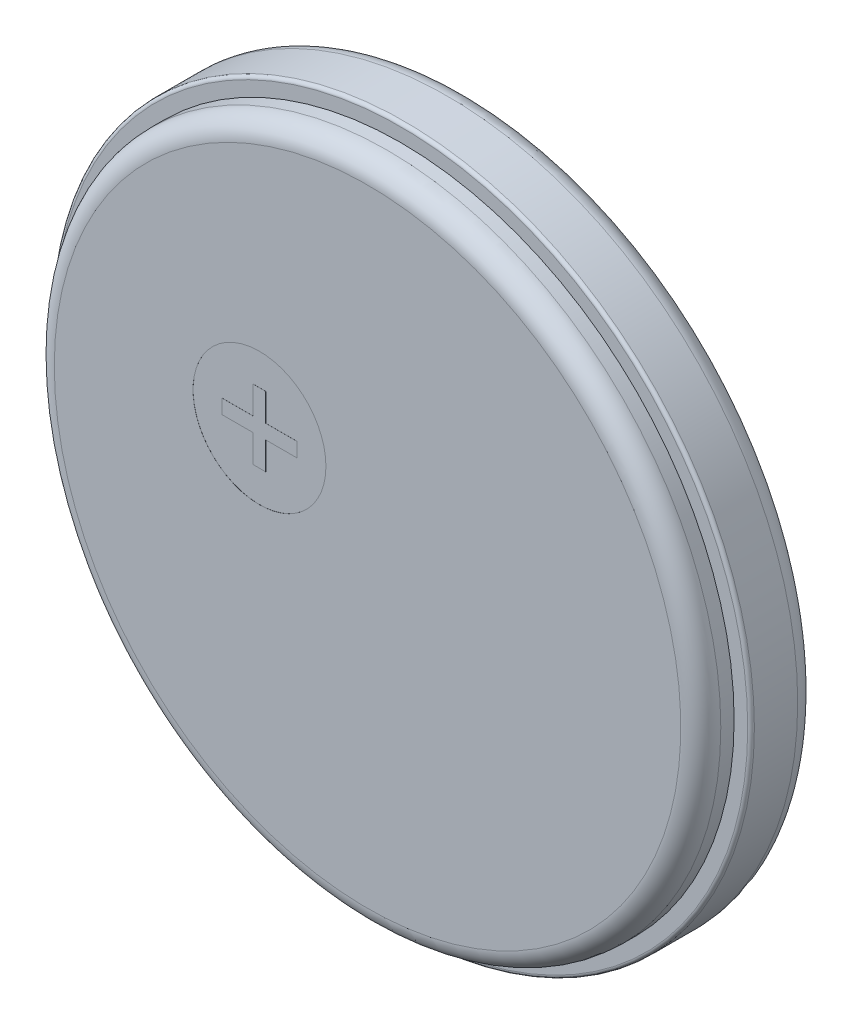
SolidWorks part; units mm, degrees
ref_plane "Front Plane" through (0, 0, 0) normal (0, 0, 1) x (1, 0, 0)
ref_plane "Top Plane" through (0, 0, 0) normal (0, 1, 0) x (1, 0, 0)
ref_plane "Right Plane" through (0, 0, 0) normal (1, 0, 0) x (0, 0, -1)
sketch "Sketch2" plane through (0, 0, 10.668) normal (0, 0, -1) x (-1, 0, 0)
  circle A0 centre (0, 31.75) radius 5
  dimension "D1" = 10
extrude "Boss-Extrude1" add sketch "Sketch2" along normal blind 0.5
fillet "Fillet1" radius 0.3 1 edges at (-5, 31.75, 10.668)
sketch "Sketch3" plane through (0, 0, 10.168) normal (0, 0, -1) x (-1, 0, 0)
  circle A2 centre (0, 31.75) radius 5.254
  circle A3 centre (0, 31.75) radius 5.254
  dimension "D1" = 0.254
extrude "Boss-Extrude2" add sketch "Sketch3" along normal blind 1
fillet "Fillet2" radius 0.3 1 edges at (-5.254, 31.75, 9.168)
fillet "Fillet3" radius 0.05 1 edges at (-5.254, 31.75, 10.168)
sketch "Sketch4" plane through (0, 0, 9.168) normal (0, 0, -1) x (-1, 0, 0)
  line L0 (-2.6501, 29.9289) -> (3.0044, 29.9289) construction
  line L1 (1.1417, 31.9299) -> (0.581, 33.5569)
  line L2 (0.581, 33.5569) -> (0.7228, 33.6419)
  line L3 (0.7228, 33.6419) -> (1.6489, 32.1001)
  line L4 (0.8246, 33.712) -> (1.7515, 32.1672)
  line L5 (0.8246, 33.712) -> (0.9402, 33.7813)
  line L6 (0.9402, 33.7813) -> (2.1566, 32.6492)
  arc A0 (1.6489, 32.1001) -> (1.7515, 32.1672) centre (0.992, 33.2168) ccw
  circle A1 centre (0.581, 33.947) radius 0.2042
  arc A3 (2.1566, 32.6492) -> (1.1417, 31.9299) centre (0.992, 33.2168) ccw
  text T0 "Lithium Ion" font "Impact" height in points 3
extrude "Cut-Extrude1" cut sketch "Sketch4" against normal blind 0.001
sketch "Sketch5" plane through (0, 0, 9.168) normal (0, 0, -1) x (-1, 0, 0)
  text T0 "Veltel" font "Century Gothic" height in points 2
extrude "Cut-Extrude2" cut sketch "Sketch5" against normal blind 0.001
sketch "Sketch6" plane through (0, 0, 9.168) normal (0, 0, -1) x (-1, 0, 0)
  text T0 "CR5505" font "Century Gothic" height in points 2
extrude "Cut-Extrude3" cut sketch "Sketch6" against normal blind 0.001
sketch "Sketch7" plane through (0, 0, 9.168) normal (0, 0, -1) x (-1, 0, 0)
  line L1 (-1.3038, 33.2168) -> (-2.5226, 33.2168)
  line L2 (-1.3038, 33.2168) -> (-1.3038, 33.4152)
  line L3 (-1.3038, 33.4152) -> (-2.5226, 33.4152)
  line L4 (-2.5226, 33.2168) -> (-2.5226, 33.4152)
  line L5 (-1.3038, 33.2168) -> (-2.5226, 33.4152) construction
  line L6 (-1.3038, 33.4152) -> (-2.5226, 33.2168) construction
  circle A0 centre (-1.9132, 33.316) radius 0.8691
  point P0 (-1.9132, 33.316)
extrude "Cut-Extrude4" cut sketch "Sketch7" against normal blind 0.001
sketch "Sketch8" plane through (0, 0, 10.668) normal (0, 0, 1) x (1, 0, 0)
  line L0 (-1.7148, 32.5891) -> (-2.1834, 32.5891)
  line L1 (-1.7148, 31.9585) -> (-1.5276, 31.9585)
  line L2 (-1.7148, 32.5891) -> (-1.7148, 33.0042)
  line L3 (-1.7148, 33.0042) -> (-1.5276, 33.0042)
  line L4 (-1.5276, 31.9585) -> (-1.5276, 32.3736)
  line L5 (-1.7148, 31.9585) -> (-1.5276, 33.0042) construction
  line L6 (-1.7148, 33.0042) -> (-1.5276, 31.9585) construction
  line L7 (-1.059, 32.3736) -> (-1.5276, 32.3736)
  line L8 (-1.059, 32.3736) -> (-1.059, 32.5891)
  line L9 (-1.059, 32.5891) -> (-1.5276, 32.5891)
  line L10 (-2.1834, 32.3736) -> (-2.1834, 32.5891)
  line L11 (-1.059, 32.3736) -> (-2.1834, 32.5891) construction
  line L12 (-1.059, 32.5891) -> (-2.1834, 32.3736) construction
  line L13 (-1.7148, 31.9585) -> (-1.7148, 32.3736)
  line L14 (-1.5276, 32.5891) -> (-1.5276, 33.0042)
  line L16 (-1.7148, 32.3736) -> (-2.1834, 32.3736)
  circle A0 centre (-1.6212, 32.4814) radius 0.9969
  point P0 (-1.6212, 32.4814)
  point P5 (-1.6212, 32.4814)
extrude "Cut-Extrude5" cut sketch "Sketch8" against normal blind 0.001
